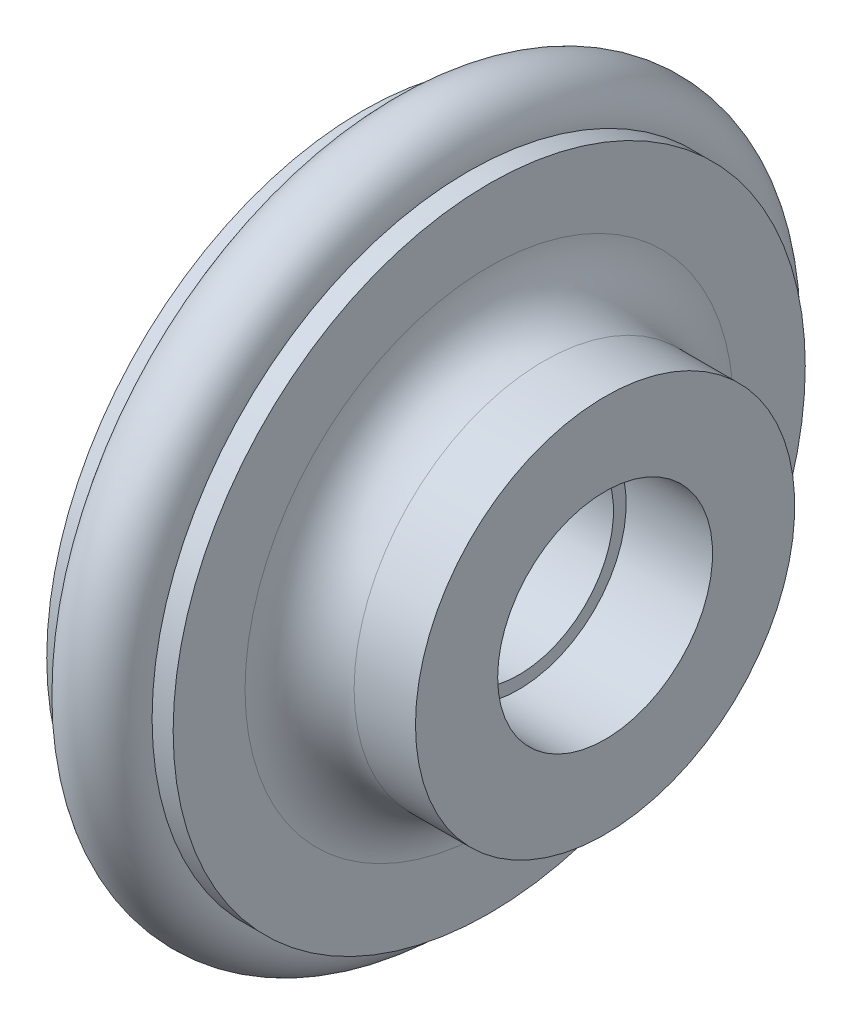
SolidWorks part; units mm, degrees
ref_plane "前视基准面" through (0, 0, 0) normal (0, 0, 1) x (1, 0, 0)
ref_plane "上视基准面" through (0, 0, 0) normal (0, 1, 0) x (1, 0, 0)
ref_plane "右视基准面" through (0, 0, 0) normal (1, 0, 0) x (0, 0, -1)
sketch "草图1" plane through (0, 0, 0) normal (0, 0, 1) x (1, 0, 0)
  line L0 (2, 15) -> (3, 15)
  line L1 (8.5, 9) -> (8.5, 5.1)
  line L2 (-3, 15) -> (-2, 15)
  line L3 (4.4, 4.5) -> (1.1, 4.5)
  line L4 (8.5, 9) -> (5.588, 9)
  line L5 (-3, 5.1) -> (1.1, 5.1)
  line L6 (1.1, 5.1) -> (1.1, 4.5)
  line L7 (0, 0) -> (4.8, 0) construction
  line L9 (8.5, 5.1) -> (4.4, 5.1)
  line L10 (4.4, 5.1) -> (4.4, 4.5)
  line L13 (3, 15) -> (3, 11.588)
  line L15 (-3, 15) -> (-3, 5.1)
  arc A0 (-2, 15) -> (2, 15) centre (0, 15) ccw
  arc A1 (5.588, 9) -> (3, 11.588) centre (5.588, 11.588) cw
  circle A2 centre (0, 15) radius 1.95
  point P9 (-2, 5.1)
  dimension "D2" = 2.588
  dimension "D9" = 9
  dimension "D3" = 15
  dimension "D10" = 6
  dimension "D7" = 2
  dimension "D13" = 3.9
  dimension "D1" = 4
  dimension "D4" = 4.5
  dimension "D5" = 4.1
  dimension "D6" = 11.5
  dimension "D8" = 5.1
  dimension "D11" = 1
  dimension "D12" = 4.1
revolve "旋转1" add sketch "草图1" angle 360 about L7
